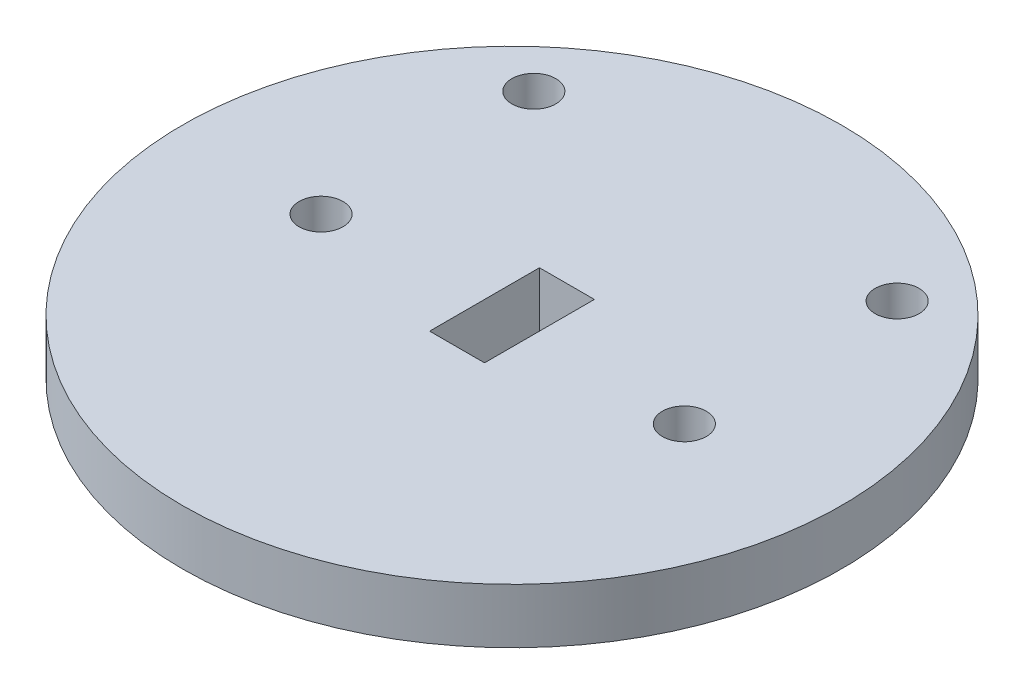
SolidWorks part; units mm, degrees
ref_plane "Front" through (0, 0, 0) normal (0, 0, 1) x (1, 0, 0)
ref_plane "Top" through (0, 0, 0) normal (0, 1, 0) x (1, 0, 0)
ref_plane "Right" through (0, 0, 0) normal (1, 0, 0) x (0, 0, -1)
sketch "Sketch1" plane through (0, 0, 0) normal (0, 1, 0) x (1, 0, 0)
  line L1 (-1.5875, -3.175) -> (1.5875, -3.175)
  line L2 (-1.5875, -3.175) -> (-1.5875, 3.175)
  line L3 (-1.5875, 3.175) -> (1.5875, 3.175)
  line L4 (1.5875, -3.175) -> (1.5875, 3.175)
  line L5 (-1.5875, -3.175) -> (1.5875, 3.175) construction
  line L6 (-1.5875, 3.175) -> (1.5875, -3.175) construction
  circle A0 centre (0, 0) radius 19.05
  dimension "D1" = 38.1
  dimension "D2" = 3.175
  dimension "D3" = 6.35
extrude "Boss-Extrude1" add sketch "Sketch1" along normal blind 3.175
sketch "Sketch2" plane through (0, 3.175, 0) normal (0, 1, 0) x (1, 0, 0)
  circle A0 centre (10.4164, -0.4545) radius 1.27
  circle A1 centre (-10.5836, -0.4545) radius 1.27
  circle A2 centre (-10.5836, 11.8455) radius 1.27
  circle A3 centre (10.4164, 11.8455) radius 1.27
  dimension "D1" = 2.54
extrude "Cut-Extrude1" cut sketch "Sketch2" against normal through all
